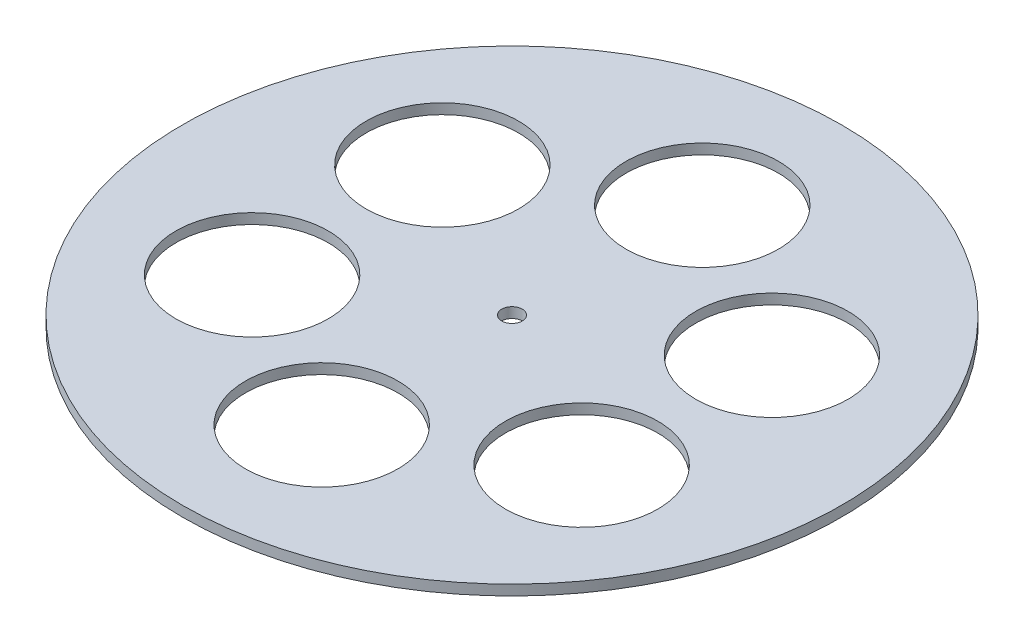
SolidWorks part; units mm, degrees
ref_plane "Front Plane" through (0, 0, 0) normal (0, 0, 1) x (1, 0, 0)
ref_plane "Top Plane" through (0, 0, 0) normal (0, 1, 0) x (1, 0, 0)
ref_plane "Right Plane" through (0, 0, 0) normal (1, 0, 0) x (0, 0, -1)
sketch "Sketch1" plane through (0, 0, 0) normal (0, 1, 0) x (1, 0, 0)
  line L1 (117.3176, 0) -> (58.6588, 101.6) construction
  line L2 (58.6588, 101.6) -> (-58.6588, 101.6) construction
  line L3 (-58.6588, 101.6) -> (-117.3176, 0) construction
  line L4 (-117.3176, 0) -> (-58.6588, -101.6) construction
  line L5 (-58.6588, -101.6) -> (58.6588, -101.6) construction
  line L6 (58.6588, -101.6) -> (117.3176, 0) construction
  line L7 (50.8, -29.3294) -> (50.8, 29.3294) construction
  line L8 (50.8, 29.3294) -> (0, 58.6588) construction
  line L9 (0, 58.6588) -> (-50.8, 29.3294) construction
  line L10 (-50.8, 29.3294) -> (-50.8, -29.3294) construction
  line L11 (-50.8, -29.3294) -> (0, -58.6588) construction
  line L12 (0, -58.6588) -> (50.8, -29.3294) construction
  circle A0 centre (0, 0) radius 101.6
  circle A1 centre (0, 0) radius 50.8 construction
  circle A2 centre (0, 0) radius 3.175
  circle A3 centre (0, 58.6588) radius 23.495
  circle A4 centre (50.8, 29.3294) radius 23.495
  circle A5 centre (50.8, -29.3294) radius 23.495
  circle A6 centre (0, -58.6588) radius 23.495
  circle A7 centre (-50.8, -29.3294) radius 23.495
  circle A8 centre (-50.8, 29.3294) radius 23.495
  point P40 (-25.4, 43.9941)
  point P41 (0, 101.6)
  dimension "D15" = 6.35
  dimension "D2" = 46.99
  dimension "D3" = 46.99
  dimension "D4" = 46.99
  dimension "D5" = 46.99
  dimension "D6" = 46.99
  dimension "D7" = 46.99
  dimension "D13" = 50.8
  dimension "D14" = 101.6
extrude "Boss-Extrude1" add sketch "Sketch1" along normal blind 3.175
